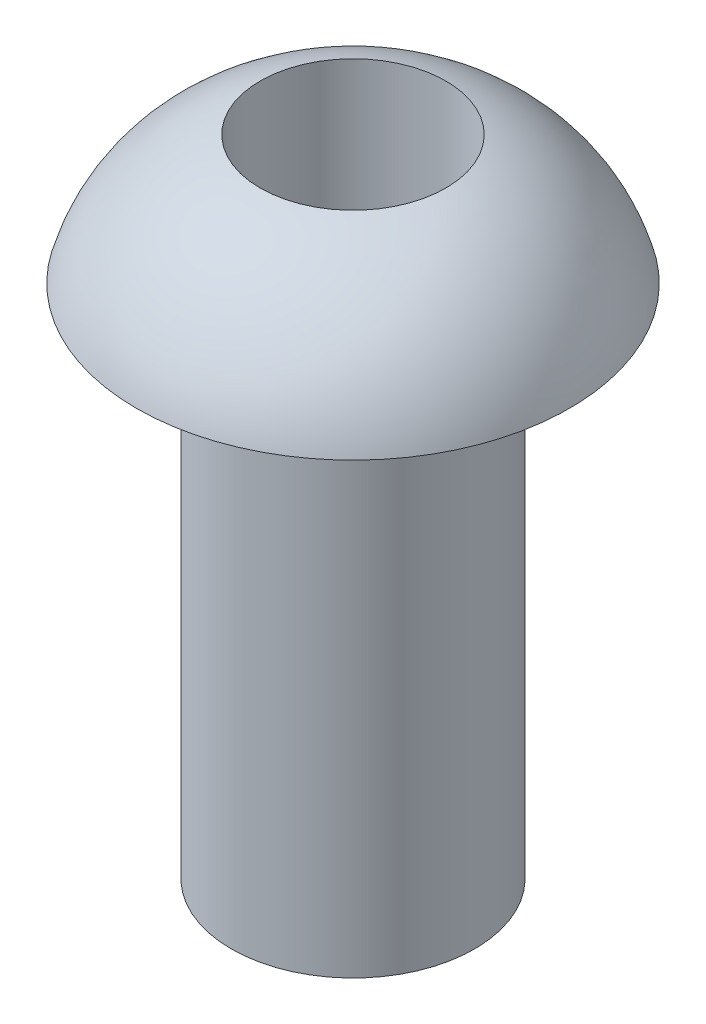
SolidWorks part; units mm, degrees
material "A-Glass Fiber"
ref_plane "Front Plane" through (0, 0, 0) normal (0, 0, 1) x (1, 0, 0)
ref_plane "Top Plane" through (0, 0, 0) normal (0, 1, 0) x (1, 0, 0)
ref_plane "Right Plane" through (0, 0, 0) normal (1, 0, 0) x (0, 0, -1)
sketch "Sketch1" plane through (0, 0, 0) normal (0, 1, 0) x (1, 0, 0)
  circle A0 centre (0, 0) radius 0.7493
  circle A1 centre (0, 0) radius 0.5715
  dimension "D1" = 1.4986
  dimension "D2" = 0.1778
extrude "Barrel" add sketch "Sketch1" along normal blind 3.175
sketch "Sketch2" plane through (0, 3.175, 0) normal (0, 1, 0) x (1, 0, 0)
  circle A0 centre (0, 0) radius 1.3335
  circle A1 centre (0, 0) radius 0.5715
  dimension "D1" = 2.667
extrude "Boss-Extrude2" add sketch "Sketch2" along normal blind 0.7937
sketch "Sketch4" plane through (0, 0, 0) normal (1, 0, 0) x (0, 0, -1)
  line L4 (1.3335, 3.9688) -> (-1.3335, 3.9688) construction
  line L5 (-1.3335, 3.175) -> (-1.3335, 3.9688)
  line L6 (-1.3335, 3.9688) -> (-0.5715, 3.9688)
  line L7 (0, 3.9688) -> (0, 0) construction
  line L8 (0.5715, 3.9688) -> (-0.5715, 3.9688) construction
  arc A0 (-0.5715, 3.9688) -> (-1.3335, 3.175) centre (-0.2324, 2.8806) ccw
revolve "Cut-Revolve11" cut sketch "Sketch4" angle 360 about L7
